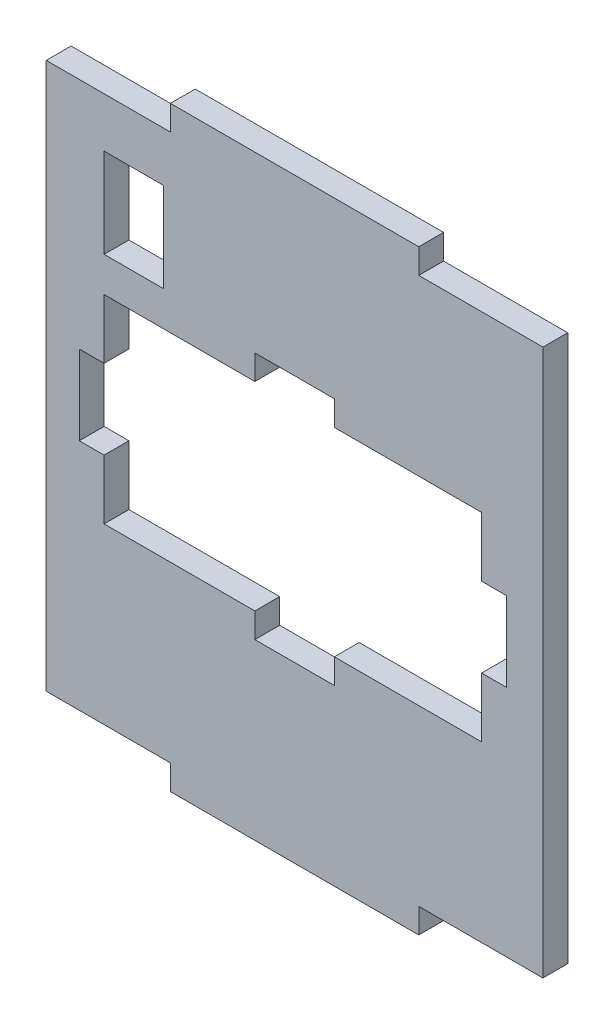
SolidWorks part; units mm, degrees
ref_plane "Front Plane" through (0, 0, 0) normal (0, 0, 1) x (1, 0, 0)
ref_plane "Top Plane" through (0, 0, 0) normal (0, 1, 0) x (1, 0, 0)
ref_plane "Right Plane" through (0, 0, 0) normal (1, 0, 0) x (0, 0, -1)
sketch "Sketch1" plane through (0, 0, 0) normal (0, 0, 1) x (1, 0, 0)
  line L0 (-78.8372, 0) -> (-43.3488, 0) construction
  line L1 (-25, 60) -> (25, 60)
  line L2 (-50, 55) -> (-50, -55)
  line L3 (-25, -60) -> (25, -60)
  line L4 (50, 55) -> (50, -55)
  line L5 (25, -55) -> (50, -55)
  line L6 (25, 55) -> (50, 55)
  line L7 (0, 56.7442) -> (0, 60) construction
  line L8 (-50, -55) -> (-25, -55)
  line L9 (-50, 55) -> (-25, 55)
  line L10 (-25, -60) -> (-25, -55)
  line L11 (25, 60) -> (25, 55)
  line L12 (-25, 55) -> (-25, 60)
  line L13 (37.6512, 8) -> (42.6512, 8)
  line L14 (0, -60) -> (0, -63.4884) construction
  line L15 (25, -55) -> (25, -60)
  line L16 (42.6512, 8) -> (42.6512, -8)
  line L17 (-38.3488, 20) -> (-8, 20)
  line L18 (-38.3488, 20) -> (-38.3488, 8)
  line L19 (-38.3488, -20) -> (-8, -20)
  line L20 (37.6512, 20) -> (37.6512, 8)
  line L21 (-0.3488, 0) -> (0, -0.1836) construction
  line L22 (-0.3488, 0) -> (0, 0.1836) construction
  line L23 (42.6512, -8) -> (37.6512, -8)
  line L24 (-38.3488, 8) -> (-43.3488, 8)
  line L25 (-43.3488, 8) -> (-43.3488, -8)
  line L26 (-43.3488, -8) -> (-38.3488, -8)
  line L27 (37.6512, -8) -> (37.6512, -20)
  line L28 (-8, -20) -> (-8, -25)
  line L29 (-8, -25) -> (8, -25)
  line L30 (8, -25) -> (8, -20)
  line L31 (-8, 20) -> (-8, 25)
  line L32 (-8, 25) -> (8, 25)
  line L33 (8, 25) -> (8, 20)
  line L34 (0, 0.1836) -> (0, -0.1836) construction
  line L35 (-0.3488, 0) -> (0, 0) construction
  line L36 (0, -25) -> (0, -32.508) construction
  line L37 (42.6512, 0) -> (78.1395, 0) construction
  line L38 (-38.3488, -8) -> (-38.3488, -20)
  line L39 (8, 20) -> (37.6512, 20)
  line L40 (8, -20) -> (37.6512, -20)
  line L41 (-38.3488, 45) -> (-38.3488, 27)
  line L42 (-38.3488, 27) -> (-26.3488, 27)
  line L43 (-26.3488, 27) -> (-26.3488, 45)
  line L44 (-26.3488, 45) -> (-38.3488, 45)
  point P0 (0, 0)
  point P4 (-0.3488, 0)
  dimension "D1" = 76
  dimension "D2" = 40
  dimension "D3" = 5
  dimension "D4" = 5
  dimension "D5" = 50
  dimension "D6" = 5
  dimension "D7" = 16
  dimension "D8" = 5
  dimension "D9" = 5
  dimension "D10" = 16
  dimension "D11" = 5
  dimension "D12" = 16
  dimension "D13" = 12
  dimension "D14" = 18
  dimension "D15" = 110
  dimension "D16" = 10
extrude "Boss-Extrude1" add sketch "Sketch1" along normal blind 5
